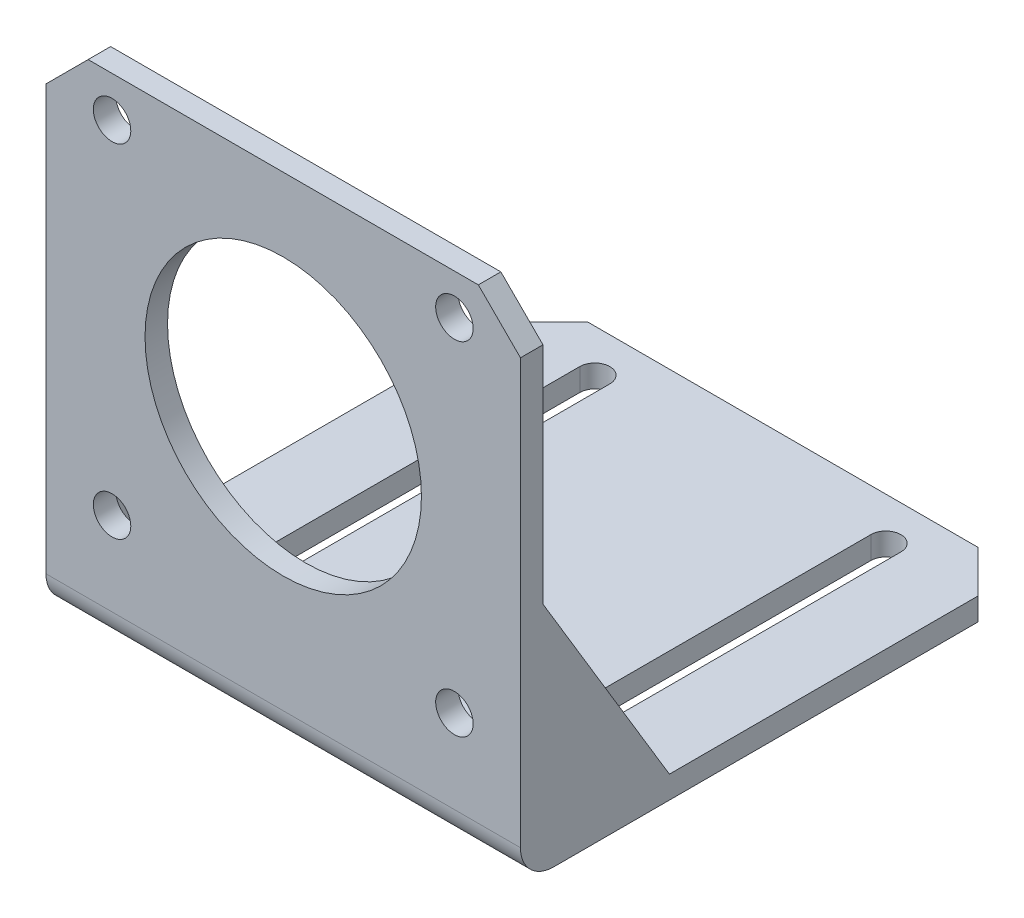
SolidWorks part; units mm, degrees
ref_plane "Front Plane" through (0, 0, 0) normal (0, 0, 1) x (1, 0, 0)
ref_plane "Top Plane" through (0, 0, 0) normal (0, 1, 0) x (1, 0, 0)
ref_plane "Right Plane" through (0, 0, 0) normal (1, 0, 0) x (0, 0, -1)
sketch "Sketch1" plane through (0, 0, 0) normal (1, 0, 0) x (0, 0, -1)
  line L2 (0, 0) -> (0, 64.22)
  line L3 (0, 64.22) -> (-3.1, 64.22)
  line L4 (-3.1, 0) -> (-3.1, 64.22)
  line L5 (0, 0) -> (-3.1, 64.22) construction
  line L6 (0, 64.22) -> (-3.1, 0) construction
  line L7 (1.48, -4.58) -> (65.7, -4.58)
  line L9 (1.48, -1.48) -> (65.7, -1.48)
  line L10 (65.7, -4.58) -> (65.7, -1.48)
  line L11 (1.48, -4.58) -> (65.7, -1.48) construction
  line L12 (1.48, -1.48) -> (65.7, -4.58) construction
  arc A0 (-3.1, 0) -> (1.48, -4.58) centre (1.48, 0) ccw
  arc A1 (0, 0) -> (1.48, -1.48) centre (1.48, 0) ccw
  point P4 (-1.55, 32.11)
  point P10 (33.59, -3.03)
  dimension "D1" = 68.8
  dimension "D2" = 3.1
  dimension "D3" = 68.8
  dimension "D4" = 4.58
extrude "Boss-Extrude1" add sketch "Sketch1" along normal blind 65.33
chamfer "Chamfer1" distance 5.8 angle 45 4 edges at (0, 64.22, 1.55) (65.33, 64.22, 1.55) (0, -3.03, -65.7) (65.33, -3.03, -65.7)
sketch "Sketch2" plane through (65.33, 0, 0) normal (1, 0, 0) x (0, 0, -1)
  line L0 (0, 27.49) -> (17.41, -1.48)
  line L1 (0, 0) -> (0, 58.42) construction
  line L2 (59.9, -1.48) -> (1.48, -1.48) construction
  line L3 (17.41, -1.48) -> (0, -1.48)
  line L4 (0, -1.48) -> (0, 27.49)
  dimension "D1" = 28.97
  dimension "D2" = 17.41
extrude "Boss-Extrude2" add sketch "Sketch2" against normal blind 2.52
sketch "Sketch3" plane through (0, 0, 0) normal (-1, 0, 0) x (0, 0, 1)
  line L0 (0, 27.49) -> (-17.41, -1.48)
  line L1 (-17.41, -1.48) -> (0, -1.48)
  line L2 (0, -1.48) -> (0, 27.49)
extrude "Boss-Extrude3" add sketch "Sketch3" against normal blind 2.52
sketch "Sketch4" plane through (0, 0, 0) normal (0, 0, -1) x (-1, 0, 0)
  line L0 (-56.235, 35.09) -> (-65.33, 35.09) construction
  line L5 (-65.33, 27.49) -> (-65.33, 58.42) construction
  line L6 (-9.095, 35.09) -> (0, 35.09) construction
  line L7 (-56.235, 58.66) -> (-9.095, 58.66) construction
  line L8 (-56.235, 58.66) -> (-56.235, 11.52) construction
  line L9 (-56.235, 11.52) -> (-9.095, 11.52) construction
  line L10 (-9.095, 58.66) -> (-9.095, 11.52) construction
  line L11 (-56.235, 58.66) -> (-9.095, 11.52) construction
  line L12 (-56.235, 11.52) -> (-9.095, 58.66) construction
  line L13 (0, 27.49) -> (0, 58.42) construction
  line L15 (-56.235, 54.12) -> (-9.095, 54.12) construction
  line L16 (-59.53, 64.22) -> (-5.8, 64.22) construction
  circle A0 centre (-32.665, 35.09) radius 19.03
  circle A1 centre (-56.235, 58.66) radius 2.58
  circle A2 centre (-9.095, 58.66) radius 2.58
  circle A3 centre (-9.095, 11.52) radius 2.58
  circle A4 centre (-56.235, 11.52) radius 2.58
  point P6 (-32.665, 35.09)
  point P11 (-32.665, 35.09)
  dimension "D2" = 38.06
  dimension "D4" = 5.16
  dimension "D5" = 5.16
  dimension "D6" = 5.16
  dimension "D7" = 5.16
  dimension "D1" = 47.14
  dimension "D3" = 10.1
extrude "Cut-Extrude1" cut sketch "Sketch4" against normal through all
sketch "Sketch5" plane through (0, -1.48, 0) normal (0, 1, 0) x (1, 0, 0)
  line L0 (52.705, 9.67) -> (52.705, 59.84) construction
  line L1 (50.635, 9.67) -> (50.635, 59.84)
  line L2 (54.775, 9.67) -> (54.775, 59.84)
  line L3 (12.625, 9.67) -> (12.625, 59.84) construction
  line L4 (10.555, 9.67) -> (10.555, 59.84)
  line L5 (14.695, 9.67) -> (14.695, 59.84)
  line L6 (54.775, 34.755) -> (65.33, 34.755) construction
  line L7 (65.33, 59.9) -> (65.33, 17.41) construction
  line L8 (10.555, 42.7015) -> (0, 42.7015) construction
  line L9 (0, 59.9) -> (0, 17.41) construction
  line L10 (52.705, 9.67) -> (12.625, 9.67) construction
  line L11 (12.625, 9.67) -> (12.625, 59.84) construction
  line L12 (12.625, 59.84) -> (52.705, 59.84) construction
  line L13 (59.53, 65.7) -> (5.8, 65.7) construction
  arc A0 (50.635, 9.67) -> (54.775, 9.67) centre (52.705, 9.67) ccw
  arc A1 (54.775, 59.84) -> (50.635, 59.84) centre (52.705, 59.84) ccw
  arc A2 (10.555, 9.67) -> (14.695, 9.67) centre (12.625, 9.67) ccw
  arc A3 (14.695, 59.84) -> (10.555, 59.84) centre (12.625, 59.84) ccw
  point P2 (52.705, 34.755)
  point P7 (12.625, 34.755)
  dimension "D1" = 4.14
  dimension "D2" = 4.14
  dimension "D3" = 35.94
  dimension "D4" = 5.86
  dimension "D5" = 50.17
extrude "Cut-Extrude2" cut sketch "Sketch5" against normal through all and the other way through all
